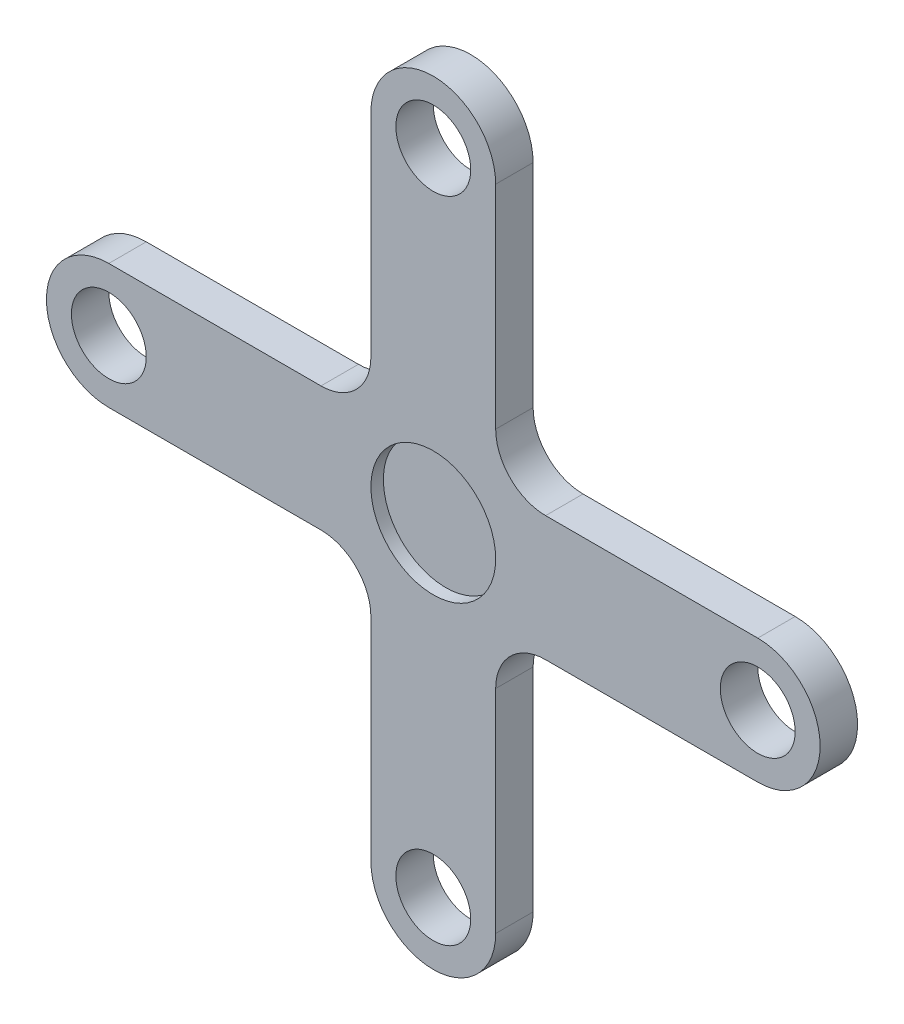
SolidWorks part; units mm, degrees
ref_plane "Ön Düzlem" through (0, 0, 0) normal (0, 0, 1) x (1, 0, 0)
ref_plane "Üst Düzlem" through (0, 0, 0) normal (0, 1, 0) x (1, 0, 0)
ref_plane "Sağ Düzlem" through (0, 0, 0) normal (1, 0, 0) x (0, 0, -1)
sketch "Çizim1" plane through (0, 0, 0) normal (0, 0, 1) x (1, 0, 0)
  line L0 (0, 0) -> (0, 13) construction
  line L1 (-2.5, -13) -> (-2.5, -4.5)
  line L2 (2.5, -13) -> (2.5, -4.5)
  line L4 (-13, 2.5) -> (-4.5, 2.5)
  line L5 (-13, -2.5) -> (-4.5, -2.5)
  line L6 (4.5, 2.5) -> (13, 2.5)
  line L7 (-2.5, 4.5) -> (-2.5, 13)
  line L8 (4.5, -2.5) -> (13, -2.5)
  line L9 (2.5, 4.5) -> (2.5, 13)
  arc A0 (-2.5, -13) -> (2.5, -13) centre (0, -13) ccw
  arc A1 (2.5, 13) -> (-2.5, 13) centre (0, 13) ccw
  arc A2 (-13, 2.5) -> (-13, -2.5) centre (-13, 0) ccw
  arc A3 (13, -2.5) -> (13, 2.5) centre (13, 0) ccw
  arc A4 (-2.5, -4.5) -> (-4.5, -2.5) centre (-4.5, -4.5) ccw
  arc A5 (4.5, -2.5) -> (2.5, -4.5) centre (4.5, -4.5) ccw
  arc A6 (2.5, 4.5) -> (4.5, 2.5) centre (4.5, 4.5) ccw
  arc A7 (-4.5, 2.5) -> (-2.5, 4.5) centre (-4.5, 4.5) ccw
  circle A8 centre (0, 13) radius 1.5
  circle A9 centre (13, 0) radius 1.5
  circle A10 centre (0, -13) radius 1.5
  circle A11 centre (-13, 0) radius 1.5
  point P2 (0, 0)
  point P9 (0, 0)
  point P28 (-2.5, 2.5)
  point P39 (0, 0)
  dimension "D3" = 2.5
  dimension "D4" = 2.5
  dimension "D5" = 2
  dimension "D6" = 3
  dimension "D1" = 26
  dimension "D2" = 26
  dimension "D7" = 4
extrude "Yükseklik-Ekstrüzyon1" add sketch "Çizim1" along normal blind 1.5
sketch "Çizim2" plane through (0, 0, 1.5) normal (0, 0, 1) x (1, 0, 0)
  circle A0 centre (0, 0) radius 2.5
  dimension "D1" = 5
extrude "Kes-Ekstrüzyon1" cut sketch "Çizim2" against normal blind 0.5
